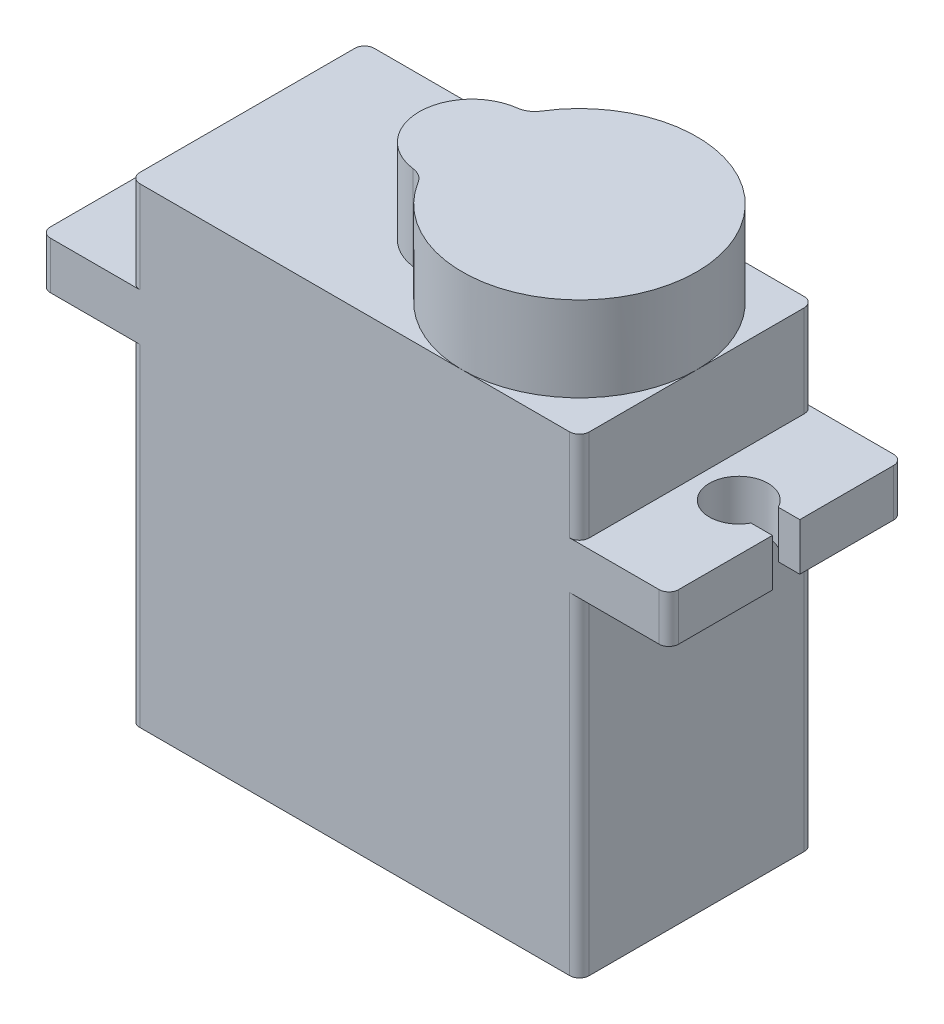
SolidWorks part; units mm, degrees
ref_plane "Front Plane" through (0, 0, 0) normal (0, 0, 1) x (1, 0, 0)
ref_plane "Top Plane" through (0, 0, 0) normal (0, 1, 0) x (1, 0, 0)
ref_plane "Right Plane" through (0, 0, 0) normal (1, 0, 0) x (0, 0, -1)
sketch "Sketch1" plane through (0, 0, 0) normal (0, 1, 0) x (1, 0, 0)
  line L1 (-11.5, -6) -> (11.5, -6)
  line L2 (-11.5, -6) -> (-11.5, 6)
  line L3 (-11.5, 6) -> (11.5, 6)
  line L4 (11.5, -6) -> (11.5, 6)
  line L5 (-11.5, -6) -> (11.5, 6) construction
  line L6 (-11.5, 6) -> (11.5, -6) construction
  point P0 (0, 0)
  dimension "D1" = 12
  dimension "D2" = 23
extrude "Boss-Extrude1" add sketch "Sketch1" along normal blind 24.1
sketch "Sketch2" plane through (0, 24.1, 0) normal (0, 1, 0) x (1, 0, 0)
  line L0 (11.5, -6) -> (11.5, 6) construction
  line L1 (11.5, 6) -> (-11.5, 6) construction
  circle A0 centre (5.5, 0) radius 6
  circle A1 centre (0, 0) radius 2.7
  dimension "D1" = 12
  dimension "D2" = 5.4
extrude "Boss-Extrude2" add sketch "Sketch2" along normal blind 4.34 contours A0 A1 | A0 A1 | A1 A0
sketch "Sketch3" plane through (0, 28.44, 0) normal (0, 1, 0) x (1, 0, 0)
  circle A0 centre (5.5, 0) radius 2.425
  dimension "D1" = 4.85
extrude "Boss-Extrude3" [suppressed] add sketch "Sketch3" along normal blind 3.24
sketch "Sketch4" plane through (0, 0, 0) normal (0, 1, 0) x (1, 0, 0)
  line L0 (11.5, 6) -> (11.5, -6)
  line L1 (11.5, 6) -> (16.075, 6)
  line L2 (11.5, -6) -> (16.075, -6)
  line L3 (16.075, 6) -> (16.075, -6)
  dimension "D1" = 4.575
extrude "Boss-Extrude4" add sketch "Sketch4" along normal blind 2.42 from offset 16.98
sketch "Sketch5" plane through (0, 19.4, 0) normal (0, 1, 0) x (1, 0, 0)
  line L0 (0, 0) -> (0, 7.9292) construction
  line L1 (14.9766, 0.7) -> (16.075, 0.7)
  line L2 (16.075, -6) -> (16.075, 6) construction
  line L3 (13.65, 0) -> (18.4745, 0) construction
  line L4 (14.9766, -0.7) -> (16.075, -0.7)
  line L5 (16.075, -0.7) -> (16.075, 0.7)
  circle A0 centre (13.65, 0) radius 1.5
  circle A1 centre (-13.65, 0) radius 1.5 construction
  line M6 (16.075, -6) -> (16.075, 6)
  dimension "D1" = 3
  dimension "D2" = 27.3
  dimension "D3" = 0.7
extrude "Cut-Extrude1" cut sketch "Sketch5" against normal up to next (2.42 mm away) contours A0 | A0 L4 L1 M6
mirror "Mirror2" about plane through (0, 0, 0) normal (1, 0, 0) of "Cut-Extrude1", "Boss-Extrude4"
fillet "Fillet1" radius 1 2 edges at (0.14, 26.27, 2.6964) (0.14, 26.27, -2.6964)
fillet "Fillet2" radius 0.5 12 edges at (16.075, 18.19, 6) (16.075, 18.19, -6) (-16.075, 18.19, -6) (-16.075, 18.19, 6) (11.5, 21.75, -6) (11.5, 8.49, -6) (-11.5, 8.49, -6) (-11.5, 21.75, -6) (11.5, 21.75, 6) (11.5, 8.49, 6) (-11.5, 21.75, 6) (-11.5, 8.49, 6)
sketch "Sketch6" plane through (0, 0, 0) normal (0, -1, 0) x (1, 0, 0)
  line L4 (-11, -6) -> (11, -6)
  line L5 (11.5, -5.5) -> (11.5, 5.5)
  line L6 (11, 6) -> (-11, 6)
  line L7 (-11.5, 5.5) -> (-11.5, -5.5)
  line L8 (-11, -6) -> (11, -6)
  line L9 (11.5, -5.5) -> (11.5, 5.5)
  line L10 (11, 6) -> (-11, 6)
  line L11 (-11.5, 5.5) -> (-11.5, -5.5)
  arc A4 (11, -6) -> (11.5, -5.5) centre (11, -5.5) ccw
  arc A5 (11.5, 5.5) -> (11, 6) centre (11, 5.5) ccw
  arc A6 (-11, 6) -> (-11.5, 5.5) centre (-11, 5.5) ccw
  arc A7 (-11.5, -5.5) -> (-11, -6) centre (-11, -5.5) ccw
  arc A8 (11, -6) -> (11.5, -5.5) centre (11, -5.5) ccw
  arc A9 (11.5, 5.5) -> (11, 6) centre (11, 5.5) ccw
  arc A10 (-11, 6) -> (-11.5, 5.5) centre (-11, 5.5) ccw
  arc A11 (-11.5, -5.5) -> (-11, -6) centre (-11, -5.5) ccw
  dimension "D1" = 0
